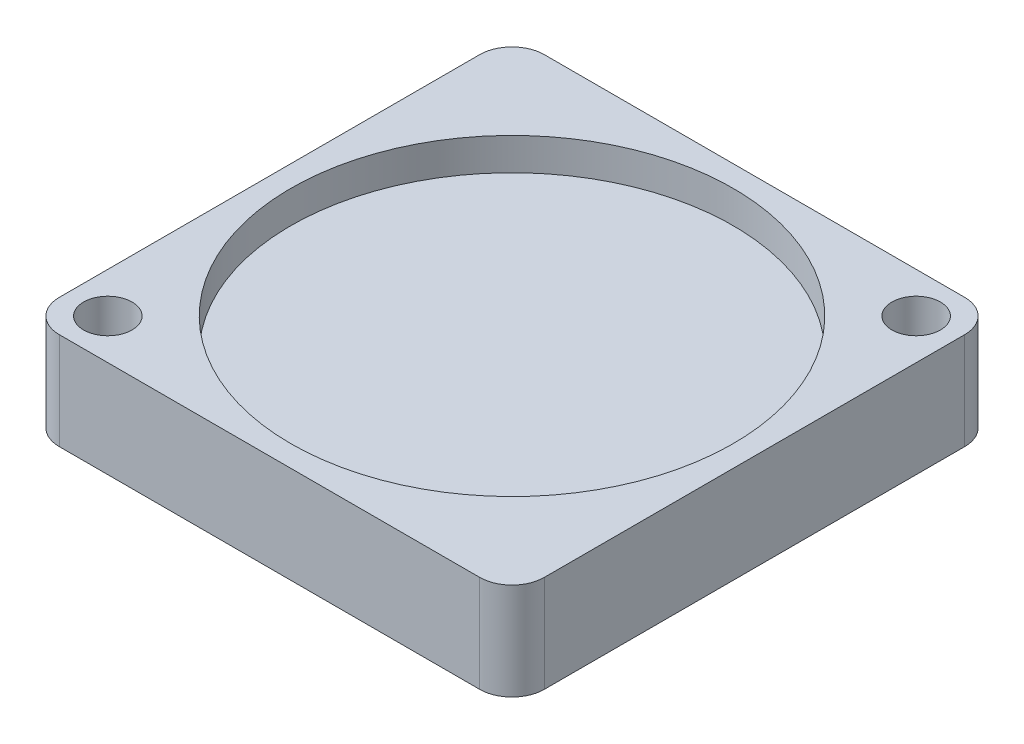
SolidWorks part; units mm, degrees
ref_plane "Front" through (0, 0, 0) normal (0, 0, 1) x (1, 0, 0)
ref_plane "Top" through (0, 0, 0) normal (0, 1, 0) x (1, 0, 0)
ref_plane "Right" through (0, 0, 0) normal (1, 0, 0) x (0, 0, -1)
sketch "草图1" plane through (0, 0, 0) normal (0, 1, 0) x (1, 0, 0)
  line L1 (7.5, -7.5) -> (-7.5, -7.5)
  line L2 (7.5, -7.5) -> (7.5, 7.5)
  line L3 (7.5, 7.5) -> (-7.5, 7.5)
  line L4 (-7.5, -7.5) -> (-7.5, 7.5)
  line L5 (7.5, -7.5) -> (-7.5, 7.5) construction
  line L6 (7.5, 7.5) -> (-7.5, -7.5) construction
  point P0 (0, 0)
  dimension "D1" = 15
  dimension "D2" = 15
extrude "凸台-拉伸1" add sketch "草图1" along normal blind 3
fillet "圆角1" radius 1 4 edges at (-7.5, 1.5, -7.5) (7.5, 1.5, -7.5) (7.5, 1.5, 7.5) (-7.5, 1.5, 7.5)
sketch "草图2" plane through (0, 3, 0) normal (0, 1, 0) x (1, 0, 0)
  line L0 (0, 9.8112) -> (0, -10.7578) construction
  line L1 (-13.8704, 0) -> (11.4312, 0) construction
  line L2 (-7.5, 6.5) -> (-7.5, -6.5) construction
  line L3 (0, 0) -> (-11.4424, 11.4424) construction
  circle A0 centre (-6.25, -6.25) radius 0.75
  circle A1 centre (6.25, 6.25) radius 0.75
  dimension "D1" = 1.5
  dimension "D2" = 6.25
  dimension "D3" = 6.25
  dimension "D4" = 45
  dimension "D5" = 12.5
  dimension "D6" = 1.25
extrude "切除-拉伸1" cut sketch "草图2" against normal through all
sketch "草图3" plane through (0, 3, 0) normal (0, 1, 0) x (1, 0, 0)
  circle A0 centre (0, 0) radius 6.8399
extrude "切除-拉伸2" cut sketch "草图3" against normal blind 1
